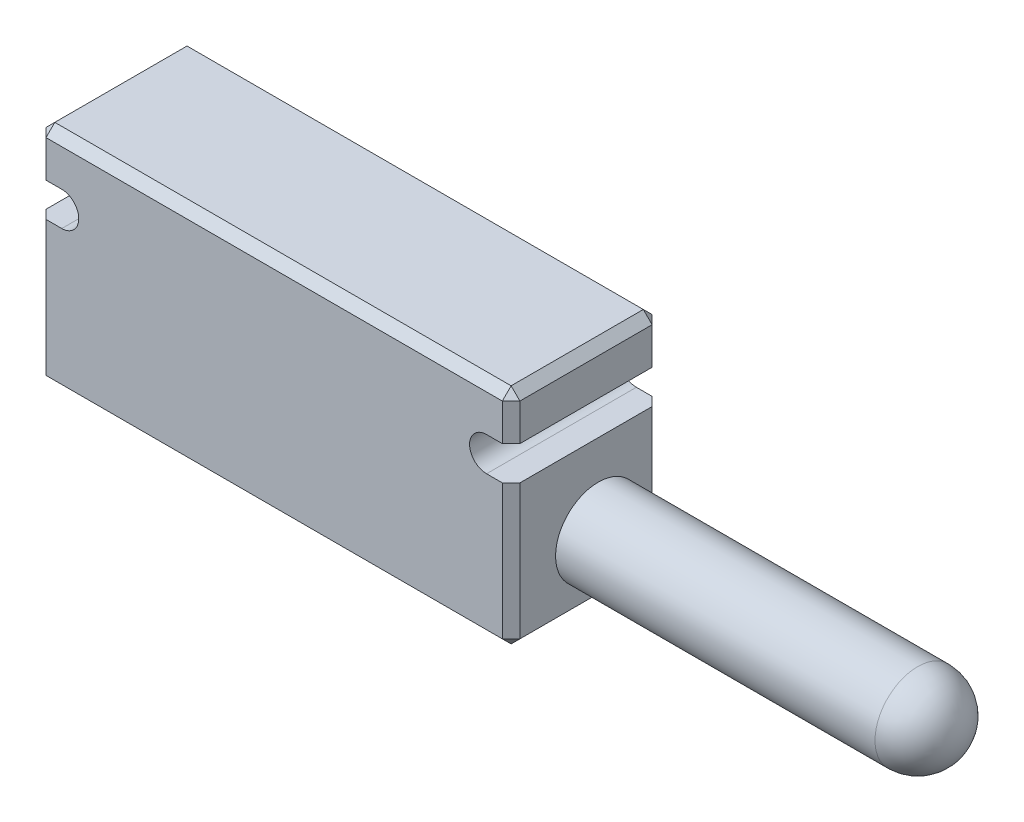
SolidWorks part; units mm, degrees
ref_plane "Front Plane" through (0, 0, 0) normal (0, 0, 1) x (1, 0, 0)
ref_plane "Top Plane" through (0, 0, 0) normal (0, 1, 0) x (1, 0, 0)
ref_plane "Right Plane" through (0, 0, 0) normal (1, 0, 0) x (0, 0, -1)
sketch "Sketch1" plane through (0, 0, 0) normal (0, 0, 1) x (1, 0, 0)
  line L1 (13.46, -6.35) -> (-13.46, -6.35)
  line L2 (13.46, -6.35) -> (13.46, 6.35)
  line L3 (13.46, 6.35) -> (-13.46, 6.35)
  line L4 (-13.46, -6.35) -> (-13.46, 6.35)
  line L5 (13.46, -6.35) -> (-13.46, 6.35) construction
  line L6 (13.46, 6.35) -> (-13.46, -6.35) construction
  point P0 (0, 0)
  dimension "D1" = 12.7
  dimension "D2" = 26.92
extrude "Boss-Extrude1" add sketch "Sketch1" along normal blind 4.95 and the other way blind 3.56
sketch "Sketch2" plane through (0, 0, 4.95) normal (0, 0, 1) x (1, 0, 0)
  line L0 (-12.065, 2.79) -> (-13.46, 2.79) construction
  line L1 (-13.46, 6.35) -> (-13.46, -6.35) construction
  line L2 (-12.065, 1.825) -> (-13.46, 1.825)
  line L3 (-12.065, 3.755) -> (-13.46, 3.755)
  line L4 (0, 0) -> (0, 6.35) construction
  line L5 (13.46, 6.35) -> (-13.46, 6.35) construction
  line L6 (12.065, 2.79) -> (13.46, 2.79) construction
  line L7 (12.065, 1.825) -> (13.46, 1.825)
  line L8 (12.065, 3.755) -> (13.46, 3.755)
  arc A0 (-12.065, 1.825) -> (-12.065, 3.755) centre (-12.065, 2.79) ccw
  arc A1 (-13.46, 3.755) -> (-13.46, 1.825) centre (-13.46, 2.79) ccw
  arc A2 (12.065, 1.825) -> (12.065, 3.755) centre (12.065, 2.79) cw
  arc A3 (13.46, 3.755) -> (13.46, 1.825) centre (13.46, 2.79) cw
  point P4 (-12.7625, 2.79)
  point P16 (12.7625, 2.79)
  dimension "D1" = 1.93
  dimension "D2" = 3.56
  dimension "D3" = 24.13
extrude "Cut-Extrude1" cut sketch "Sketch2" against normal through all
sketch "Sketch3" plane through (13.46, 0, 0) normal (1, 0, 0) x (0, 0, -1)
  line L0 (3.56, -6.35) -> (-4.95, -6.35) construction
  circle A0 centre (0, -2.79) radius 2.425
  dimension "D1" = 4.85
  dimension "D2" = 3.56
extrude "Boss-Extrude2" add sketch "Sketch3" along normal blind 20.57
fillet "Fillet1" radius 2.425 1 edges at (34.03, -2.79, -2.425)
chamfer "Chamfer1" distance 0.5 angle 45 15 edges at (13.46, 6.35, 0.695) (13.46, 5.0525, -3.56) (0, 6.35, -3.56) (-13.46, 6.35, 0.695) (13.46, 5.0525, 4.95) (0, 6.35, 4.95) (-13.46, 5.0525, 4.95) (13.46, -6.35, 0.695) (-13.46, -2.2625, -3.56) (13.46, -2.2625, -3.56) (0, -6.35, -3.56) (-13.46, -6.35, 0.695) (13.46, -2.2625, 4.95) (0, -6.35, 4.95) (-13.46, -2.2625, 4.95)
